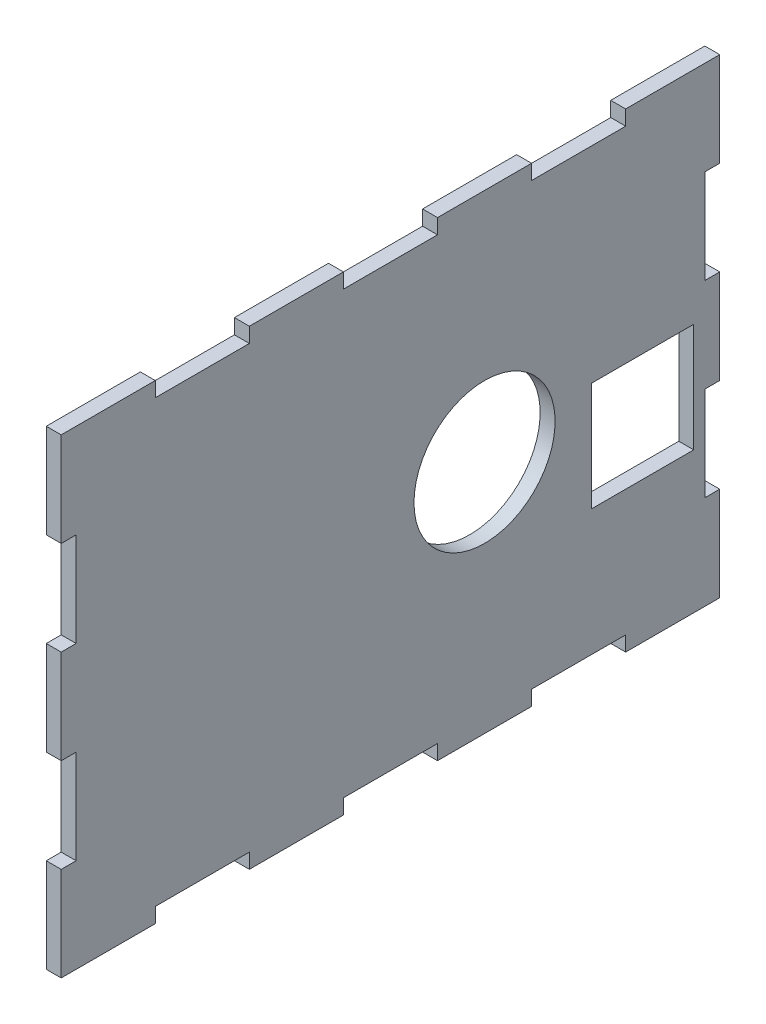
SolidWorks part; units mm, degrees
material "Acrylic (Medium-high impact)"
ref_plane "Front Plane" through (0, 0, 0) normal (0, 0, 1) x (1, 0, 0)
ref_plane "Top Plane" through (0, 0, 0) normal (0, 1, 0) x (1, 0, 0)
ref_plane "Right Plane" through (0, 0, 0) normal (1, 0, 0) x (0, 0, -1)
sketch "Sketch46" plane through (0, 0, 0) normal (-1, 0, 0) x (0, 0, 1)
  line L1 (625.3769, 3.125) -> (603.6319, 3.125)
  line L3 (738.1019, 50) -> (598.1019, 50)
  line L4 (738.1019, 50) -> (738.1019, -49.9999)
  line L5 (738.1019, -49.9999) -> (598.1019, -49.9999)
  line L6 (598.1019, 50) -> (598.1019, -49.9999)
  line L9 (625.3769, 3.125) -> (625.3769, -20)
  line L10 (603.6319, 3.125) -> (603.6319, -20)
  line L11 (603.6319, -20) -> (625.3769, -20)
  circle A0 centre (648.1019, 0) radius 15
extrude "Boss-Extrude11" add sketch "Sketch46" along normal blind 3.175 separate body
sketch "Sketch47" plane through (-3.175, 0, 0) normal (-1, 0, 0) x (0, 0, 1)
  line L0 (738.1019, -10) -> (738.1019, -30)
  line L1 (738.1019, -49.9999) -> (738.1019, 50) construction
  line L2 (738.1019, -10) -> (734.9269, -10)
  line L3 (734.9269, -10) -> (734.9269, -30)
  line L4 (738.1019, 30) -> (734.9269, 30)
  line L5 (738.1019, 30) -> (738.1019, 10)
  line L6 (738.1019, 10) -> (734.9269, 10)
  line L7 (734.9269, 30) -> (734.9269, 10)
  line L8 (738.1019, -30) -> (734.9269, -30)
  line L9 (598.1019, -10) -> (598.1019, -30)
  line L10 (598.1019, 50) -> (598.1019, -49.9999) construction
  line L11 (598.1019, -10) -> (601.2769, -10)
  line L12 (601.2769, -10) -> (601.2769, -30)
  line L13 (598.1019, 30) -> (601.2769, 30)
  line L14 (598.1019, 30) -> (598.1019, 10)
  line L15 (598.1019, 10) -> (601.2769, 10)
  line L16 (601.2769, 30) -> (601.2769, 10)
  line L17 (598.1019, -30) -> (601.2769, -30)
  line L18 (678.1019, 50) -> (678.1019, 46.825)
  line L19 (738.1019, 50) -> (598.1019, 50) construction
  line L20 (678.1019, 50) -> (658.1019, 50)
  line L21 (658.1019, 50) -> (658.1019, 46.825)
  line L22 (718.1019, 50) -> (698.1019, 50)
  line L23 (718.1019, 50) -> (718.1019, 46.825)
  line L24 (718.1019, 46.825) -> (698.1019, 46.825)
  line L25 (698.1019, 50) -> (698.1019, 46.825)
  line L26 (678.1019, 46.825) -> (658.1019, 46.825)
  line L27 (638.1019, 50) -> (638.1019, 46.825)
  line L28 (638.1019, 50) -> (618.1019, 50)
  line L29 (618.1019, 50) -> (618.1019, 46.825)
  line L30 (638.1019, 46.825) -> (618.1019, 46.825)
  line L31 (678.1019, -49.9999) -> (678.1019, -46.8249)
  line L32 (598.1019, -49.9999) -> (738.1019, -49.9999) construction
  line L33 (678.1019, -49.9999) -> (658.1019, -49.9999)
  line L34 (658.1019, -49.9999) -> (658.1019, -46.8249)
  line L35 (718.1019, -49.9999) -> (698.1019, -49.9999)
  line L36 (718.1019, -49.9999) -> (718.1019, -46.8249)
  line L37 (718.1019, -46.8249) -> (698.1019, -46.8249)
  line L38 (698.1019, -49.9999) -> (698.1019, -46.8249)
  line L39 (678.1019, -46.8249) -> (658.1019, -46.8249)
  line L40 (638.1019, -49.9999) -> (638.1019, -46.8249)
  line L41 (638.1019, -49.9999) -> (618.1019, -49.9999)
  line L42 (618.1019, -49.9999) -> (618.1019, -46.8249)
  line L43 (638.1019, -46.8249) -> (618.1019, -46.8249)
  dimension "D1" = 2
  dimension "D2" = 2
  dimension "D3" = 3
  dimension "D4" = 3
extrude "Cut-Extrude23" cut sketch "Sketch47" against normal blind 3.175
